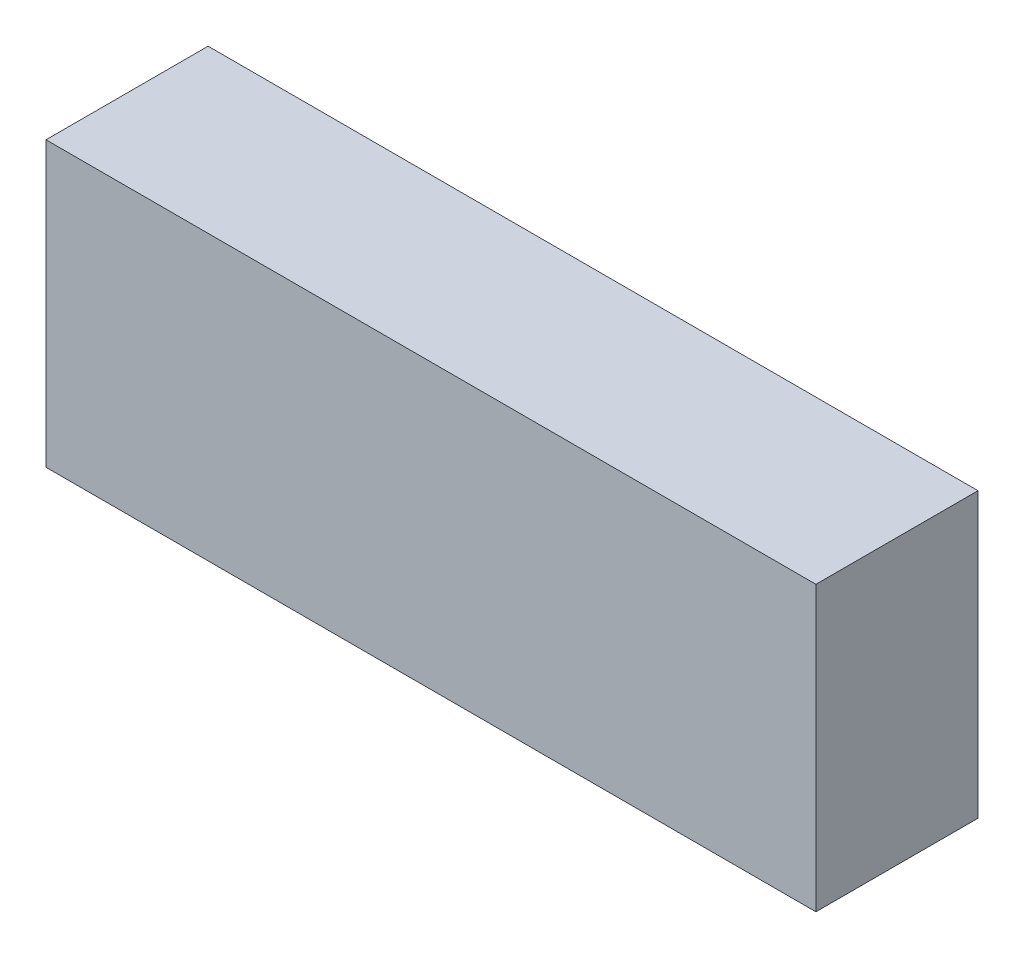
SolidWorks part; units mm, degrees
material "Rubber"
ref_plane "Спереди" through (0, 0, 0) normal (0, 0, 1) x (1, 0, 0)
ref_plane "Сверху" through (0, 0, 0) normal (0, 1, 0) x (1, 0, 0)
ref_plane "Справа" through (0, 0, 0) normal (1, 0, 0) x (0, 0, -1)
sketch "Sketch1" plane through (0, 0, 0) normal (0, 0, 1) x (1, 0, 0)
  line L1 (-19, -7) -> (19, -7)
  line L2 (-19, -7) -> (-19, 7)
  line L3 (-19, 7) -> (19, 7)
  line L4 (19, -7) -> (19, 7)
  line L5 (-19, -7) -> (19, 7) construction
  line L6 (-19, 7) -> (19, -7) construction
  point P0 (0, 0)
  dimension "D1" = 38
  dimension "D2" = 14
extrude "Boss-Extrude1" add sketch "Sketch1" along normal blind 8
